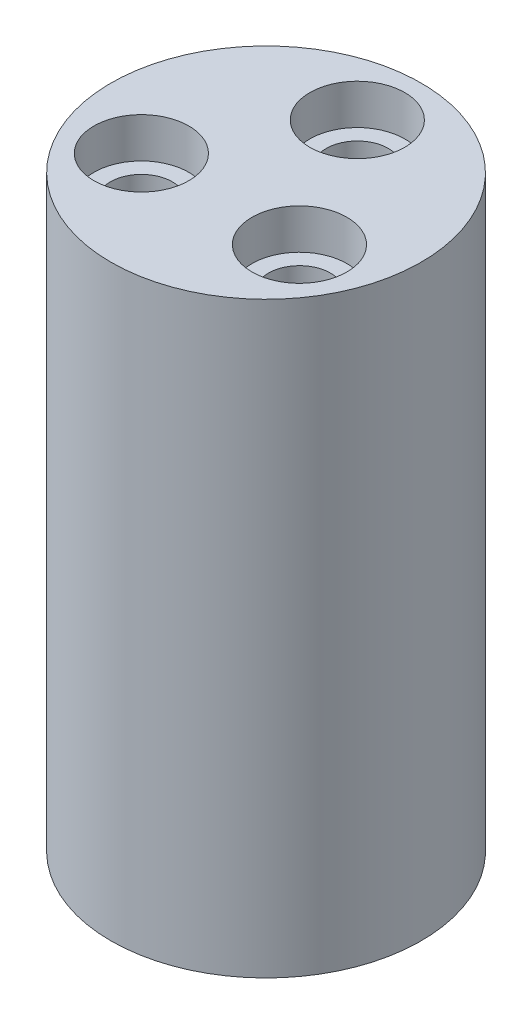
SolidWorks part; units mm, degrees
ref_plane "Front Plane" through (0, 0, 0) normal (0, 0, 1) x (1, 0, 0)
ref_plane "Top Plane" through (0, 0, 0) normal (0, 1, 0) x (1, 0, 0)
ref_plane "Right Plane" through (0, 0, 0) normal (1, 0, 0) x (0, 0, -1)
sketch "Sketch1" plane through (0, 0, 0) normal (0, 1, 0) x (1, 0, 0)
  line L0 (0, 0) -> (0, 5) construction
  circle A0 centre (0, 0) radius 8.5
  circle A1 centre (0, 5) radius 1.7
  circle A2 centre (4.3301, -2.5) radius 1.7
  circle A3 centre (-4.3301, -2.5) radius 1.7
  point P11 (0, 0)
  dimension "D1" = 17
  dimension "D2" = 3.4
  dimension "D3" = 5
  dimension "D4" = 3
extrude "Boss-Extrude1" add sketch "Sketch1" along normal blind 32.2
sketch "Sketch2" plane through (0, 32.2, 0) normal (0, 1, 0) x (1, 0, 0)
  circle A0 centre (0, 5) radius 2.6
  circle A1 centre (4.3301, -2.5) radius 2.6
  circle A2 centre (-4.3301, -2.5) radius 2.6
  dimension "D1" = 5.2
extrude "Cut-Extrude1" cut sketch "Sketch2" against normal blind 2.2
